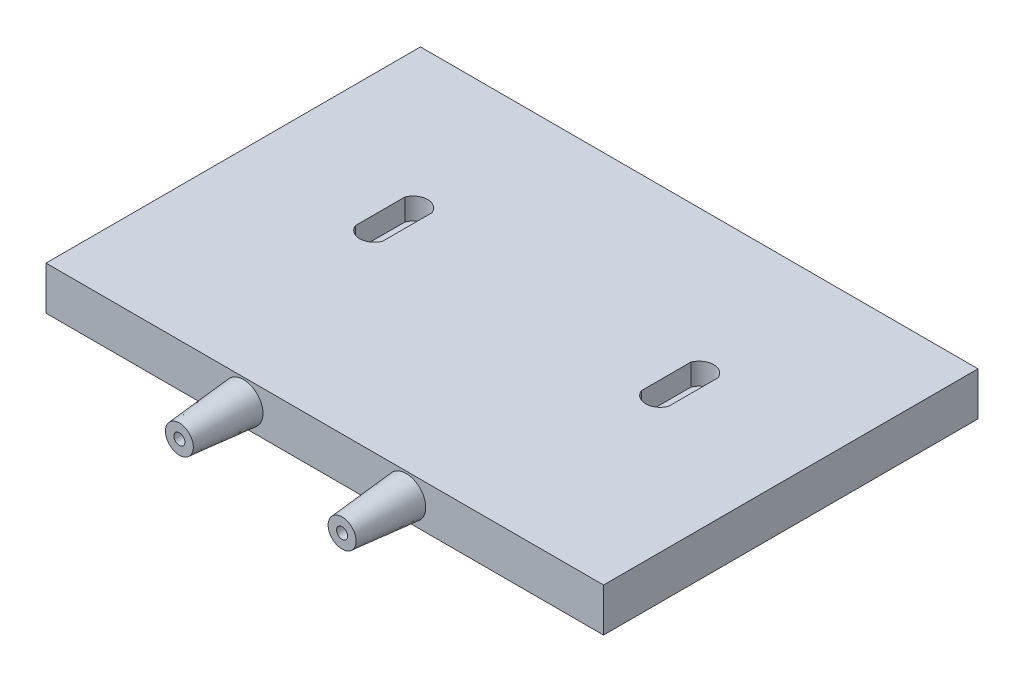
SolidWorks part; units mm, degrees
ref_plane "正面" through (0, 0, 0) normal (0, 0, 1) x (1, 0, 0)
ref_plane "平面" through (0, 0, 0) normal (0, 1, 0) x (1, 0, 0)
ref_plane "右側面" through (0, 0, 0) normal (1, 0, 0) x (0, 0, -1)
sketch "ｽｹｯﾁ1" plane through (0, 0, 0) normal (0, 1, 0) x (1, 0, 0)
  line L1 (-78.375, 52.636) -> (78.375, 52.636)
  line L2 (-78.375, 52.636) -> (-78.375, -52.636)
  line L3 (-78.375, -52.636) -> (78.375, -52.636)
  line L4 (78.375, 52.636) -> (78.375, -52.636)
  line L5 (-78.375, 52.636) -> (78.375, -52.636) construction
  line L6 (-78.375, -52.636) -> (78.375, 52.636) construction
  point P0 (0, 0)
  dimension "D1" = 156.75
  dimension "D2" = 105.272
extrude "ﾎﾞｽ - 押し出し1" add sketch "ｽｹｯﾁ1" along normal blind 12.2
ref_plane "平面1" through (0, 12.2, 0) normal (0, 1, 0) x (1, 0, 0)
sketch "ｽｹｯﾁ2" plane through (0, 12.2, 0) normal (0, 1, 0) x (1, 0, 0)
  line L1 (44.016, 0) -> (36.3764, 0)
  line L2 (44.016, 13.8901) -> (36.3764, 13.8901)
  line L3 (-44.016, 13.8901) -> (-36.3764, 13.8901)
  line L4 (-44.016, 13.8901) -> (-44.016, 0)
  line L5 (-44.016, 0) -> (-36.3764, 0)
  line L6 (-36.3764, 13.8901) -> (-36.3764, 0)
  line L7 (-44.016, 13.8901) -> (-36.3764, 0) construction
  line L8 (-44.016, 0) -> (-36.3764, 13.8901) construction
  line L9 (0, 52.636) -> (0, -52.636) construction
  line L10 (78.375, 52.636) -> (-78.375, 52.636) construction
  line L11 (-78.375, -52.636) -> (78.375, -52.636) construction
  line L12 (44.016, 13.8901) -> (44.016, 0)
  line L13 (36.3764, 13.8901) -> (36.3764, 0)
  arc A0 (-44.016, 13.8901) -> (-36.3764, 13.8901) centre (-40.1962, 12.4004) cw
  arc A1 (-44.016, 0) -> (-36.3764, 0) centre (-40.1962, 1.4897) ccw
  arc A2 (44.016, 0) -> (36.3764, 0) centre (40.1962, 1.4897) cw
  arc A3 (44.016, 13.8901) -> (36.3764, 13.8901) centre (40.1962, 12.4004) ccw
  point P0 (-40.1962, 6.9451)
  dimension "D3" = 52.636
extrude "ｶｯﾄ - 押し出し1" cut sketch "ｽｹｯﾁ2" against normal blind 6.1 contours A0 L3 | L6 L3 L4 L5 | L5 A1 | L2 A3 | L2 L13 L1 L12 | A2 L1
ref_plane "平面2" through (0, 0, 52.636) normal (0, 0, 1) x (1, 0, 0)
sketch "ｽｹｯﾁ4" plane through (0, 0, 52.636) normal (0, 0, 1) x (1, 0, 0)
  line L0 (0, 12.2) -> (0, 0) construction
  line L1 (-78.375, 12.2) -> (78.375, 12.2) construction
  line L2 (-78.375, 0) -> (78.375, 0) construction
  line L3 (-78.375, 12.2) -> (-78.375, 0) construction
  circle A0 centre (-22.875, 6.1) radius 5.5
  circle A2 centre (22.875, 6.1) radius 5.5
  dimension "D1" = 6.1
  dimension "D3" = 11
  dimension "D2" = 55.5
extrude "ﾎﾞｽ - 押し出し2" add sketch "ｽｹｯﾁ4" along normal blind 18 draft 5 contours A0 | A2
sketch "ｽｹｯﾁ6" plane through (0, 0, 52.636) normal (0, 0, 1) x (1, 0, 0)
  line L0 (0, 12.2) -> (0, 0) construction
  line L1 (-78.375, 12.2) -> (78.375, 12.2) construction
  line L2 (-78.375, 0) -> (78.375, 0) construction
  circle A0 centre (-22.875, 6.1) radius 1.55
  circle A1 centre (22.875, 6.1) radius 1.55
  dimension "D1" = 3.1
extrude "ｶｯﾄ - 押し出し2" cut sketch "ｽｹｯﾁ6" along normal up to next
sketch "ｽｹｯﾁ7" plane through (0, 0, 0) normal (0, 1, 0) x (1, 0, 0)
  line L0 (0, -52.636) -> (0, -72.6331) construction
  line L1 (-26.375, -60.636) -> (-19.375, -60.636)
  line L2 (-26.375, -60.636) -> (-26.375, -57.136)
  line L3 (-26.375, -57.136) -> (-19.375, -57.136)
  line L4 (-19.375, -60.636) -> (-19.375, -57.136)
  line L5 (-6.71, -52.636) -> (6.71, -52.636) construction
  line L6 (-26.8002, -70.636) -> (-18.9498, -70.636) construction
  line L7 (-26.8002, -70.636) -> (-26.375, -60.636) construction
  line L8 (-18.9498, -70.636) -> (-19.375, -60.636) construction
  line L9 (19.375, -60.636) -> (19.375, -57.136)
  line L10 (26.375, -57.136) -> (19.375, -57.136)
  line L11 (26.375, -60.636) -> (26.375, -57.136)
  line L12 (26.375, -60.636) -> (19.375, -60.636)
  dimension "D1" = 7
  dimension "D2" = 3.5
  dimension "D3" = 10
extrude "ｶｯﾄ - 押し出し3" cut sketch "ｽｹｯﾁ7" along normal blind 9.1
